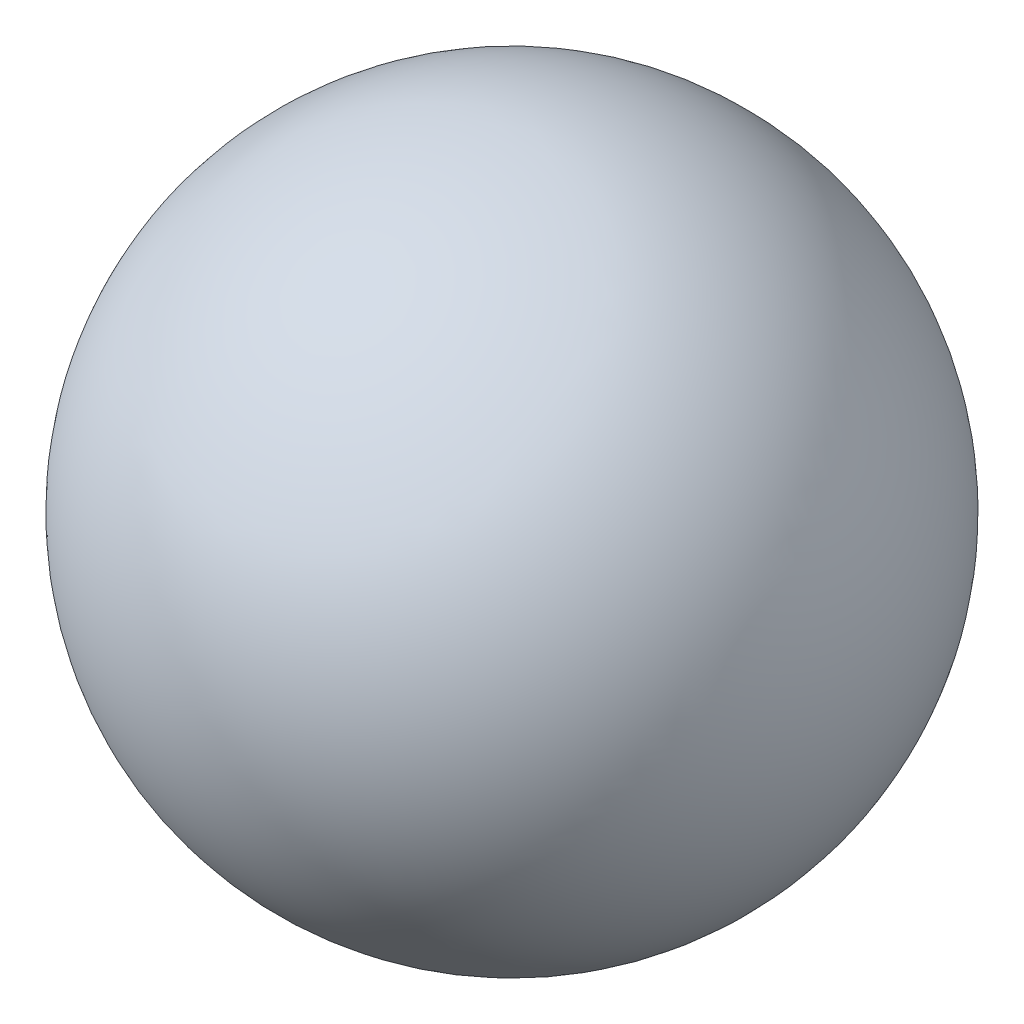
SolidWorks part; units mm, degrees
ref_plane "Front Plane" through (0, 0, 0) normal (0, 0, 1) x (1, 0, 0)
ref_plane "Top Plane" through (0, 0, 0) normal (0, 1, 0) x (1, 0, 0)
ref_plane "Right Plane" through (0, 0, 0) normal (1, 0, 0) x (0, 0, -1)
sketch "Sketch1" plane through (0, 0, 0) normal (0, 0, 1) x (1, 0, 0)
  line L0 (-12, 0) -> (12, 0)
  arc A0 (12, 0) -> (-12, 0) centre (0, 0) cw
  point P4 (0, 0)
  dimension "D1" = 24
revolve "Revolve1" add sketch "Sketch1" angle 360 about L0
